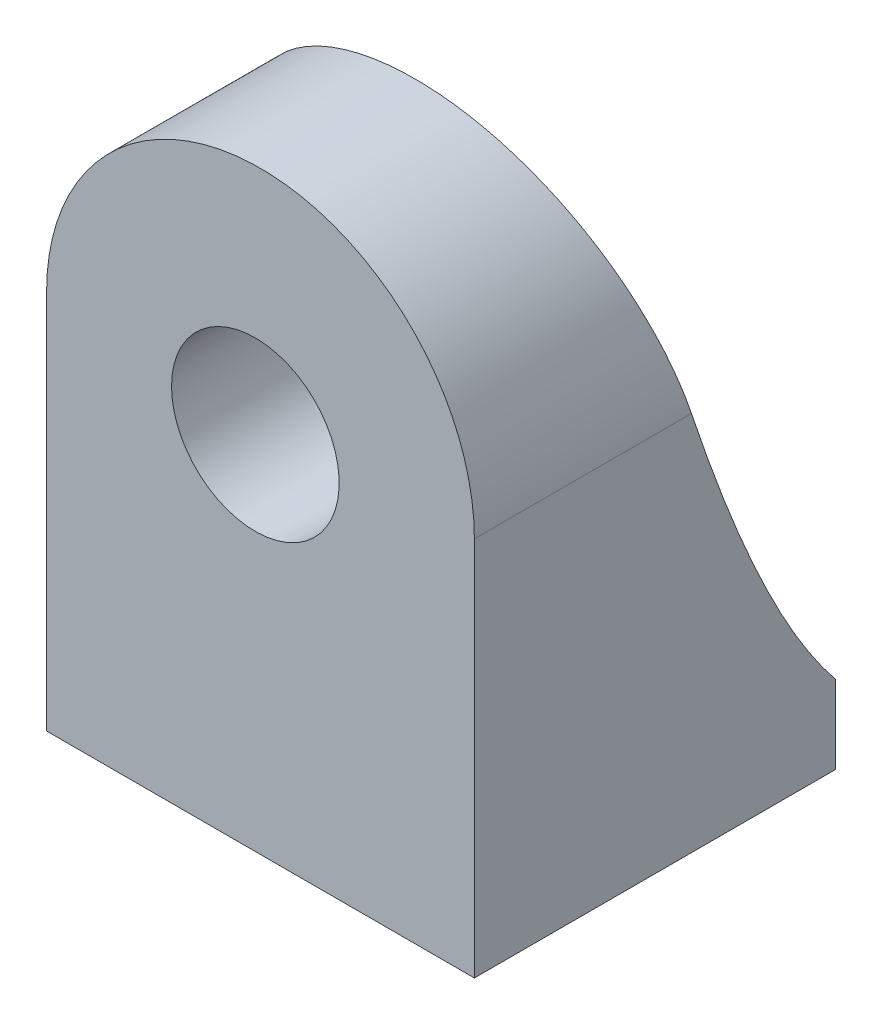
SolidWorks part; units mm, degrees
ref_plane "Front Plane" through (0, 0, 0) normal (0, 0, 1) x (1, 0, 0)
ref_plane "Top Plane" through (0, 0, 0) normal (0, 1, 0) x (1, 0, 0)
ref_plane "Right Plane" through (0, 0, 0) normal (1, 0, 0) x (0, 0, -1)
sketch "Sketch1" plane through (0, 0, 0) normal (0, 0, 1) x (1, 0, 0)
  line L0 (-66.5758, -33.8276) -> (-33.9125, -33.8276) construction
  line L1 (-33.9125, -33.8276) -> (-33.9125, 11.9656) construction
  line L2 (-10.1213, -4.3276) -> (-10.1213, -33.8276)
  line L3 (-50.1172, 12.1672) -> (-52.3535, 12.1672) construction
  line L4 (-52.3535, 12.1672) -> (-45.9283, 12.1671) construction
  line L5 (-45.9283, 12.1671) -> (-33.9125, 12.1671) construction
  line L6 (-33.9125, 12.1671) -> (-33.9125, 11.9656) construction
  line L7 (-52.3535, 12.1672) -> (-66.7491, 12.1675) construction
  line L8 (-66.7491, 12.1675) -> (-66.7491, -32.9927) construction
  line L9 (-10.1213, -33.8276) -> (23.0559, -33.8276)
  line L10 (23.0559, -33.8276) -> (23.0559, -4.3276)
  arc A0 (23.0559, -4.3276) -> (-10.1213, -4.3276) centre (6.4673, -4.3276) ccw
extrude "Boss-Extrude1" add sketch "Sketch1" along normal blind 28
sketch "Sketch3" plane through (23.0559, 0, 0) normal (1, 0, 0) x (0, 0, -1)
  line L0 (0, -33.8276) -> (0, -4.3276) construction
  line L1 (0, 12.2611) -> (-28, 12.2611) construction
  line L2 (0, -4.3276) -> (0, 12.2611) construction
  line L3 (0, -7.6714) -> (0, -27.7389)
  line L6 (0, 12.2611) -> (-16, 12.2611)
  line L11 (0, -7.6714) -> (0, 12.2611)
  spline S0 degree 2 poles (0, -27.7389) (-8.2135, -17.7736) (-16, 12.2611) knots 0 0 0 1 1 1
  dimension "D1" = 40
extrude "Cut-Extrude1" cut sketch "Sketch3" against normal through all
sketch "Sketch5" plane through (0, 0, 0) normal (0, 0, -1) x (-1, 0, 0)
  line L0 (10.1213, -33.8276) -> (-23.0559, -33.8276) construction
  line L5 (-20.0559, -28.8276) -> (-20.0559, -5.8276)
  line L6 (-23.0559, -5.8276) -> (-20.0559, -5.8276) construction
  line L7 (-23.0559, -4.3276) -> (-23.0559, -27.7389) construction
  line L8 (10.1213, -27.7389) -> (10.1213, -4.3276) construction
  line L9 (7.1213, -5.8276) -> (7.1213, -28.8276)
  line L10 (-20.0559, -28.8276) -> (7.1213, -28.8276)
  line L11 (7.1213, -5.8276) -> (10.1213, -5.8276) construction
  arc A0 (7.1213, -5.8276) -> (-20.0559, -5.8276) centre (-6.4673, -5.8276) ccw
  dimension "D1" = 5
extrude "Cut-Extrude2" cut sketch "Sketch5" against normal blind 17
sketch "Sketch7" plane through (0, 0, 0) normal (0, 0, -1) x (-1, 0, 0)
  line L0 (-6.0687, -33.8276) -> (-6.0687, -5.8276) construction
  line L1 (10.1213, -33.8276) -> (-23.0559, -33.8276) construction
  circle A0 centre (-6.0687, -5.8276) radius 6.5
  dimension "D1" = 13
extrude "Cut-Extrude3" cut sketch "Sketch7" against normal through all
sketch "Sketch8" plane through (0, -28.8276, 0) normal (0, 1, 0) x (1, 0, 0)
  line L0 (20.0559, -8.5) -> (-7.1213, -8.5) construction
  line L1 (20.0559, -17) -> (20.0559, 0) construction
  line L2 (-7.1213, -17) -> (-7.1213, 0) construction
  circle A0 centre (6.4673, -8.5) radius 7
extrude "Cut-Extrude4" cut sketch "Sketch8" against normal blind 10
